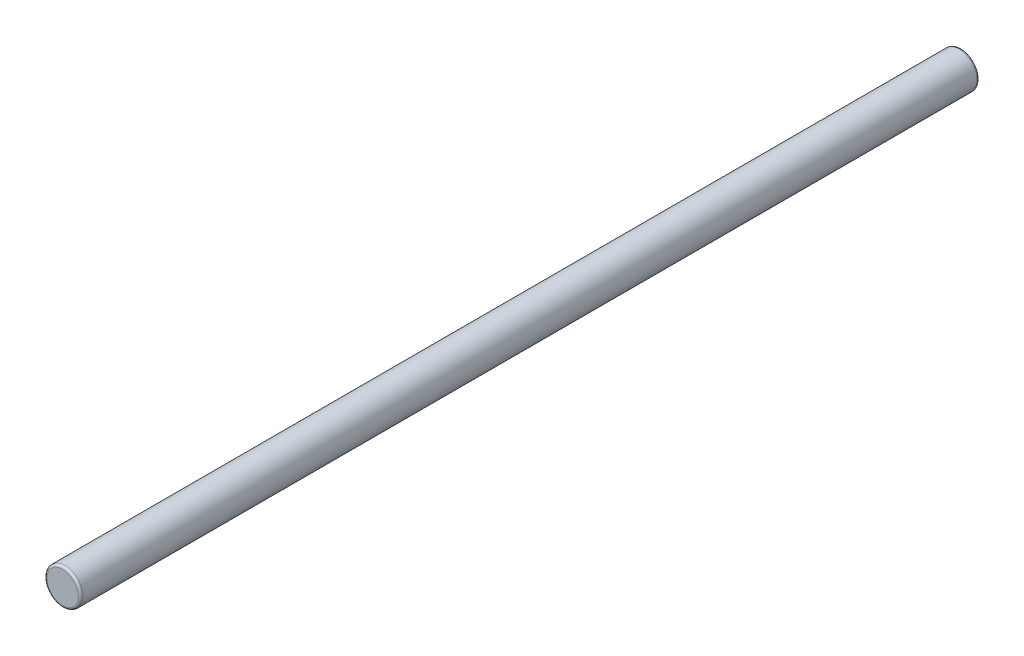
SolidWorks part; units mm, degrees
ref_plane "Front Plane" through (0, 0, 0) normal (0, 0, 1) x (1, 0, 0)
ref_plane "Top Plane" through (0, 0, 0) normal (0, 1, 0) x (1, 0, 0)
ref_plane "Right Plane" through (0, 0, 0) normal (1, 0, 0) x (0, 0, -1)
sketch "Sketch1" plane through (0, 0, 0) normal (0, 0, 1) x (1, 0, 0)
  circle A0 centre (0, 0) radius 4
  dimension "D1" = 8
extrude "Boss-Extrude1" add sketch "Sketch1" along normal blind 200
fillet "Fillet1" radius 0.5 2 edges at (4, 0, 0) (4, 0, 200)
